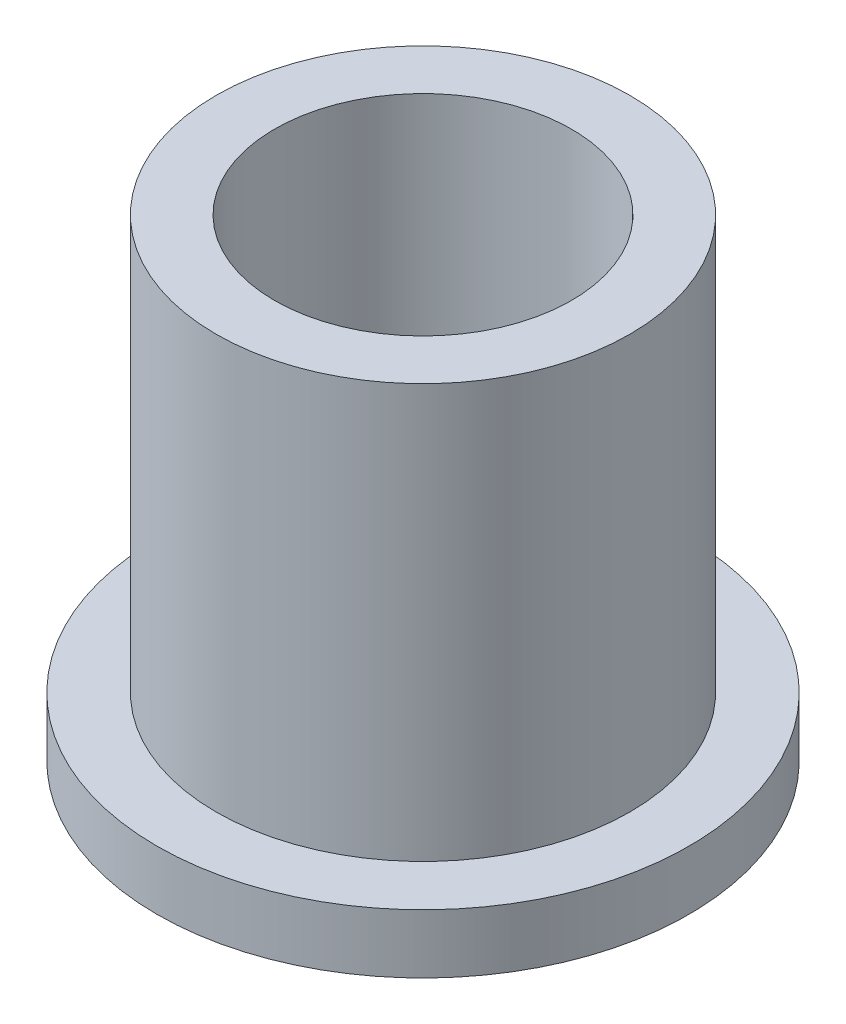
SolidWorks part; units mm, degrees
ref_plane "Front" through (0, 0, 0) normal (0, 0, 1) x (1, 0, 0)
ref_plane "Top" through (0, 0, 0) normal (0, 1, 0) x (1, 0, 0)
ref_plane "Right" through (0, 0, 0) normal (1, 0, 0) x (0, 0, -1)
sketch "Sketch1" plane through (0, 0, 0) normal (0, 1, 0) x (1, 0, 0)
  circle A0 centre (0, 0) radius 3.9878
  circle A1 centre (0, 0) radius 5.5562
  circle A2 centre (0, 0) radius 7.1438
  dimension "ID" = 7.9756
  dimension "OD" = 11.1125
  dimension "FlangeOD" = 14.2875
sketch "Sketch2" plane through (0, 0, 0) normal (0, 1, 0) x (1, 0, 0)
  circle A0 centre (0, 0) radius 3.9878 construction
  circle A1 centre (0, 0) radius 5.5562 construction
  circle A2 centre (0, 0) radius 3.9878
  circle A3 centre (0, 0) radius 5.5562
extrude "Boss-Extrude1" add sketch "Sketch2" along normal blind 12.7
sketch "Sketch3" plane through (0, 0, 0) normal (0, 1, 0) x (1, 0, 0)
  circle A0 centre (0, 0) radius 7.1438 construction
  circle A1 centre (0, 0) radius 5.5562 construction
  circle A2 centre (0, 0) radius 7.1438
  circle A3 centre (0, 0) radius 5.5562
extrude "Boss-Extrude2" add sketch "Sketch3" along normal blind 1.5875
